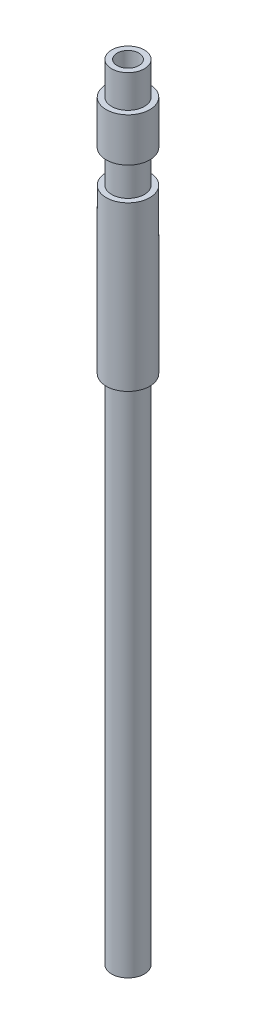
SolidWorks part; units mm, degrees
material "Простая углеродистая сталь"
ref_plane "Спереди" through (0, 0, 0) normal (0, 0, 1) x (1, 0, 0)
ref_plane "Сверху" through (0, 0, 0) normal (0, 1, 0) x (1, 0, 0)
ref_plane "Справа" through (0, 0, 0) normal (1, 0, 0) x (0, 0, -1)
sketch "Эскиз1" plane through (0, 0, 0) normal (0, 1, 0) x (1, 0, 0)
  circle A0 centre (0, 0) radius 1
  circle A1 centre (0, 0) radius 2
  dimension "D1" = 4
  dimension "D2" = 2
extrude "Бобышка-Вытянуть1" add sketch "Эскиз1" along normal blind 72
sketch "Эскиз2" plane through (0, 0, 0) normal (0, 0, 1) x (1, 0, 0)
  line L0 (2, 72) -> (1.5, 72)
  line L1 (2, 72) -> (2, 69)
  line L2 (1.5, 72) -> (1.5, 69)
  line L3 (2, 69) -> (1.5, 69)
  line L4 (2, 65) -> (1.5, 65)
  line L5 (2, 65) -> (2, 62)
  line L6 (1.5, 65) -> (1.5, 62)
  line L7 (2, 62) -> (1.5, 62)
  line L8 (1, 72) -> (-1, 72) construction
  line L9 (1, 72) -> (-1, 72) construction
  line L10 (0, 72) -> (0, 0) construction
  line L11 (-2, 0) -> (2, 0) construction
  line L12 (-2, 0) -> (2, 0) construction
  dimension "D1" = 3
  dimension "D2" = 0.5
  dimension "D3" = 2
  dimension "D4" = 7
revolve "Вырез-Повернуть1" cut sketch "Эскиз2" angle 360 about L10
sketch "Эскиз3" plane through (0, 0, 0) normal (0, 0, 1) x (1, 0, 0)
  line L0 (2, 0) -> (1.5, 0)
  line L1 (2, 0) -> (2, 47)
  line L2 (1.5, 0) -> (1.5, 47)
  line L3 (2, 47) -> (1.5, 47)
  line L4 (2, 62) -> (-2, 62) construction
  line L5 (0, 0) -> (0, 72) construction
  line L6 (1, 72) -> (-1, 72) construction
  line L7 (1, 72) -> (-1, 72) construction
  dimension "D1" = 15
  dimension "D2" = 0.5
revolve "Вырез-Повернуть2" cut sketch "Эскиз3" angle 360 about L5
sketch "Эскиз4" plane through (0, 0, 0) normal (0, 0, 1) x (1, 0, 0)
  line L0 (-2, 60) -> (2, 60) construction
  line L1 (1.5, 72) -> (-1.5, 72) construction
  line L2 (1.5, 72) -> (-1.5, 72) construction
  line L3 (2, 62) -> (-2, 62) construction
  line L4 (2, 62) -> (-2, 62) construction
  line L5 (-2, 62) -> (-2, 47) construction
  line L6 (2, 47) -> (2, 62) construction
  dimension "D1" = 12
ref_plane "Плоскость1" through (0, 60, 0) normal (0, 1, 0) x (1, 0, 0)
sketch "Эскиз5" plane through (0, 60, 0) normal (0, 1, 0) x (1, 0, 0)
  line L0 (-2, 0) -> (2, 0) construction
  circle A0 centre (0, 0) radius 2 construction
